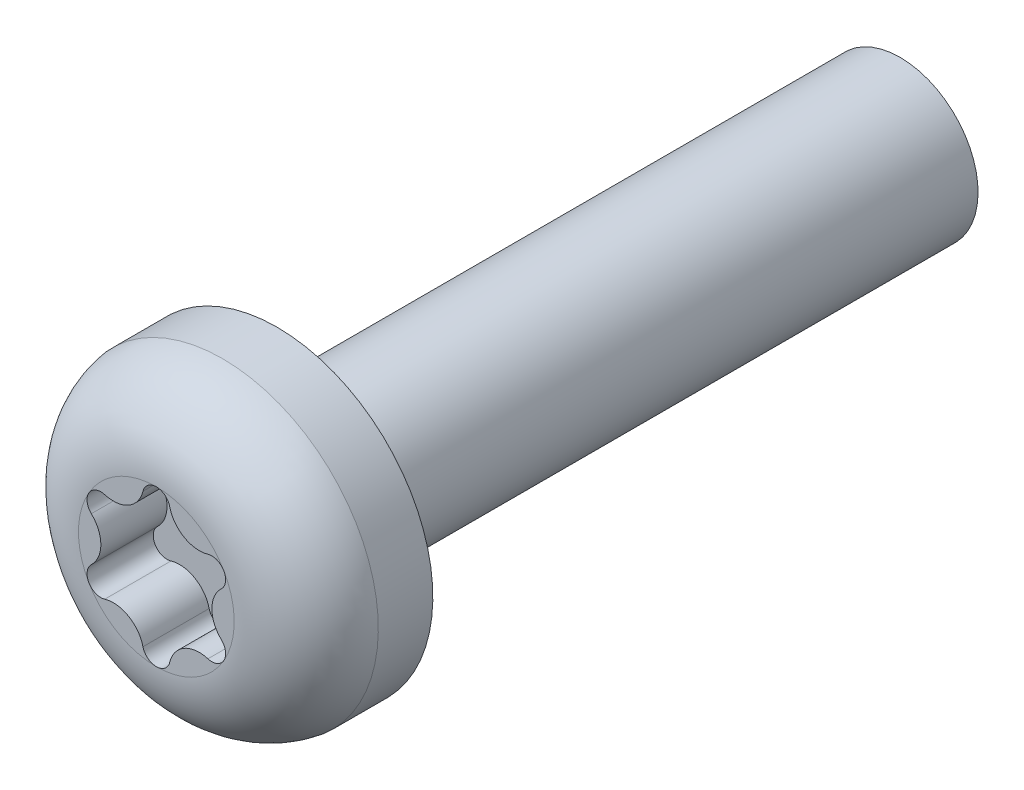
SolidWorks part; units mm, degrees
material "AISI Acier à outil type A2"
ref_plane "Face" through (0, 0, 0) normal (0, 0, 1) x (1, 0, 0)
ref_plane "Dessus" through (0, 0, 0) normal (0, 1, 0) x (1, 0, 0)
ref_plane "Droite" through (0, 0, 0) normal (1, 0, 0) x (0, 0, -1)
sketch "Esquisse1" plane through (0, 0, 0) normal (1, 0, 0) x (0, 0, -1)
  line L0 (-3.1, 0) -> (-3.1, 2)
  line L1 (-1.4, 4) -> (0, 4)
  line L2 (0, 4) -> (0, 2)
  line L3 (0, 2) -> (16, 2)
  line L4 (16, 2) -> (16, 0)
  line L5 (16, 0) -> (-3.1, 0)
  line L6 (-3.1, 0) -> (-4.3313, 0) construction
  arc A0 (-3.1, 2) -> (-1.4, 4) centre (-1.0735, 2) cw
  dimension "L" = 16
  dimension "K" = 3.1
  dimension "T" = 1.7
  dimension "M" = 4
  dimension "DH" = 8
  dimension "A" = 4
revolve "Révolution1" add sketch "Esquisse1" angle 360 about L6
cosmetic thread "Représentation de filetage1" parameters "D2"=3.1
sketch "Esquisse2" plane through (0, 0, 3.1) normal (0, 0, 1) x (1, 0, 0)
  line L0 (0, -1.0692) -> (0, 1.0844) construction
  line L1 (0, 0) -> (-0.1844, 0.9269) construction
  line L2 (0, 0) -> (0.1807, 0.9086) construction
  line L3 (0, 0) -> (0.8195, 0.4731) construction
  line L4 (0, 0) -> (0.7063, 0.6194) construction
  line L5 (0, 0) -> (0.3928, 0.6804) construction
  line L7 (0, 1.6463) -> (-1.4258, 0.8232) construction
  line L8 (-1.4258, 0.8232) -> (-1.4258, -0.8232) construction
  line L9 (-1.4258, -0.8232) -> (0, -1.6463) construction
  line L10 (0, -1.6463) -> (1.4258, -0.8232) construction
  line L11 (1.4258, -0.8232) -> (1.4258, 0.8232) construction
  line L12 (1.4258, 0.8232) -> (0, 1.6463) construction
  circle A0 centre (0, 0) radius 2 construction
  circle A1 centre (0, 0) radius 2 construction
  arc A2 (-0.3439, 1.7289) -> (0.3439, 1.7289) centre (0, 1.6463) cw
  circle A3 centre (0, 0) radius 1.4258 construction
  arc A4 (0.3439, 1.7289) -> (1.3253, 1.1623) centre (1.1034, 1.9112) ccw
  arc A5 (1.3253, 1.1623) -> (1.6692, 0.5666) centre (1.4258, 0.8232) cw
  arc A6 (1.6692, 0.5666) -> (1.6692, -0.5666) centre (2.2069, 0) ccw
  arc A7 (1.6692, -0.5666) -> (1.3253, -1.1623) centre (1.4258, -0.8232) cw
  arc A8 (1.3253, -1.1623) -> (0.3439, -1.7289) centre (1.1034, -1.9112) ccw
  arc A9 (0.3439, -1.7289) -> (-0.3439, -1.7289) centre (0, -1.6463) cw
  arc A10 (-0.3439, -1.7289) -> (-1.3253, -1.1623) centre (-1.1034, -1.9112) ccw
  arc A11 (-1.3253, -1.1623) -> (-1.6692, -0.5666) centre (-1.4258, -0.8232) cw
  arc A12 (-1.6692, -0.5666) -> (-1.6692, 0.5666) centre (-2.2069, 0) ccw
  arc A13 (-1.6692, 0.5666) -> (-1.3253, 1.1623) centre (-1.4258, 0.8232) cw
  arc A14 (-1.3253, 1.1623) -> (-0.3439, 1.7289) centre (-1.1034, 1.9112) ccw
  point P22 (0.7129, 1.2347)
  dimension "D1" = 22.5
  dimension "D2" = 60
  dimension "D3" = 11.25
  dimension "D4" = 6
extrude "Enlèv. mat.-Extru.1" cut sketch "Esquisse2" against normal blind 1.7
equation "\"D3@Esquisse2\" = \"D1@Esquisse2\"/2"
equation "\"D1@Enlèv. mat.-Extru.1\" = \"T@Esquisse1\""
